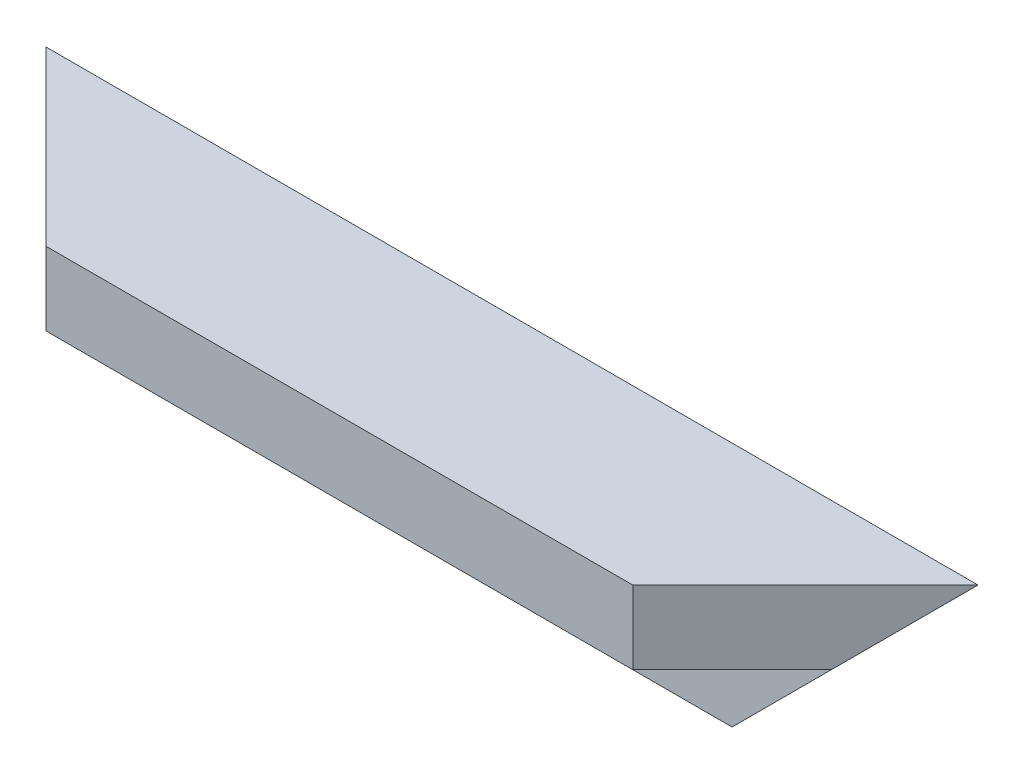
SolidWorks part; units mm, degrees
ref_plane "Plan de face" through (0, 0, 0) normal (0, 0, 1) x (1, 0, 0)
ref_plane "Plan de dessus" through (0, 0, 0) normal (0, 1, 0) x (1, 0, 0)
ref_plane "Plan de droite" through (0, 0, 0) normal (1, 0, 0) x (0, 0, -1)
sketch "Esquisse1" plane through (0, 0, 0) normal (1, 0, 0) x (0, 0, -1)
  line L0 (0, 0) -> (-40, 0)
  line L1 (-40, 0) -> (-40, -17)
  line L2 (-40, -17) -> (-17, -17)
  line L3 (-17, -17) -> (-17, -40)
  line L4 (-17, -40) -> (0, -40)
  line L5 (0, -40) -> (0, 0)
  dimension "D1" = 40
  dimension "D2" = 17
extrude "Boss.-Extru.1" add sketch "Esquisse1" along normal up to vertex (216 mm away)
sketch "Esquisse2" plane through (0, 0, 0) normal (0, 1, 0) x (1, 0, 0)
  line L0 (216, 0) -> (176, -40)
  line L1 (216, -40) -> (0, -40) construction
  line L2 (176, -40) -> (216, -40)
  line L3 (216, -40) -> (216, 0)
  line L4 (0, 0) -> (0, -40)
  line L5 (0, -40) -> (40, -40)
  line L6 (40, -40) -> (0, 0)
extrude "Enlèv. mat.-Extru.1" cut sketch "Esquisse2" against normal through all
sketch "Esquisse3" plane through (0, 0, 0) normal (0, 0, -1) x (-1, 0, 0)
  line L0 (-216, 0) -> (-176, -40)
  line L1 (-216, -40) -> (0, -40) construction
  line L2 (-176, -40) -> (-216, -40)
  line L3 (-216, -40) -> (-216, 0)
  line L4 (-40, -40) -> (0, -40)
  line L5 (0, -40) -> (0, 0)
  line L6 (0, 0) -> (-40, -40)
extrude "Enlèv. mat.-Extru.2" cut sketch "Esquisse3" against normal through all
